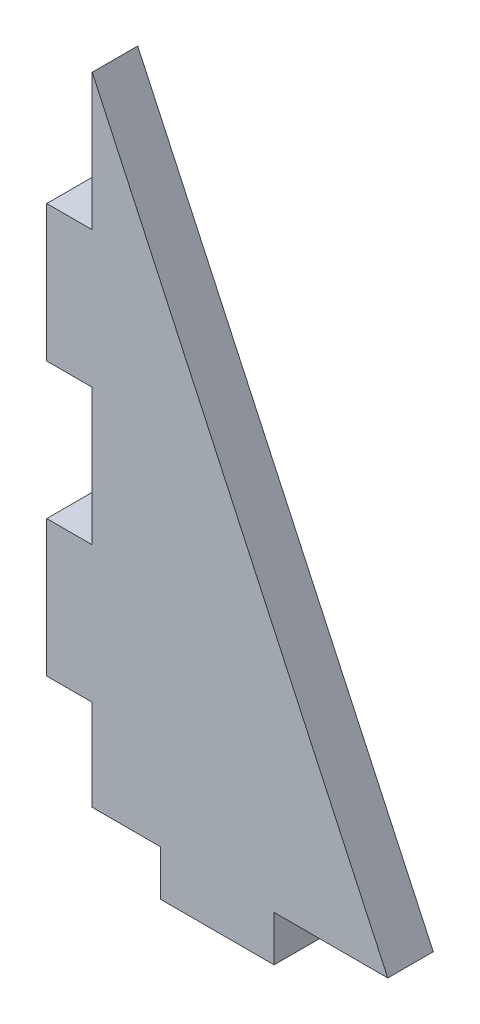
SolidWorks part; units mm, degrees
ref_plane "Front Plane" through (0, 0, 0) normal (0, 0, 1) x (1, 0, 0)
ref_plane "Top Plane" through (0, 0, 0) normal (0, 1, 0) x (1, 0, 0)
ref_plane "Right Plane" through (0, 0, 0) normal (1, 0, 0) x (0, 0, -1)
sketch "Sketch1" plane through (0, 0, 0) normal (0, 0, 1) x (1, 0, 0)
  line L12 (0, 0) -> (0, 76.2)
  line L16 (0, 76.2) -> (5.08, 76.2)
  line L18 (5.08, 76.2) -> (38.1, 5.08)
  line L19 (38.1, 5.08) -> (38.1, 0)
  line L20 (38.1, 0) -> (0, 0)
  dimension "D1" = 5.08
  dimension "D2" = 76.2
  dimension "D3" = 38.1
extrude "Boss-Extrude1" add sketch "Sketch1" along normal blind 5.08
sketch "Sketch2" plane through (0, 0, 5.08) normal (0, 0, 1) x (1, 0, 0)
  line L0 (5.08, 76.2) -> (5.08, 60.96)
  line L1 (5.08, 60.96) -> (5.08, 45.72) construction
  line L2 (5.08, 45.72) -> (5.08, 30.48)
  line L3 (5.08, 30.48) -> (5.08, 15.24) construction
  line L4 (5.08, 15.24) -> (5.08, 0)
  line L5 (0, 0) -> (38.1, 0) construction
  line L6 (5.08, 15.24) -> (0, 15.24)
  line L7 (0, 76.2) -> (0, 0) construction
  line L8 (5.08, 30.48) -> (0, 30.48)
  line L9 (5.08, 45.72) -> (0, 45.72)
  line L10 (5.08, 60.96) -> (0, 60.96)
  line L11 (5.08, 76.2) -> (0, 76.2)
  line L12 (0, 76.2) -> (0, 60.96)
  line L13 (0, 45.72) -> (0, 30.48)
  line L14 (0, 15.24) -> (0, 0)
  line L15 (0, 0) -> (5.08, 0)
  line L16 (38.1, 5.08) -> (25.4, 5.08)
  line L17 (25.4, 5.08) -> (12.7, 5.08) construction
  line L18 (12.7, 5.08) -> (0, 5.08)
  line L19 (12.7, 5.08) -> (12.7, 0)
  line L20 (25.4, 5.08) -> (25.4, 0)
  line L21 (12.7, 0) -> (0, 0)
  line L22 (25.4, 0) -> (38.1, 0)
  line L23 (38.1, 0) -> (38.1, 5.08)
  line M12 (0, 0) -> (38.1, 0)
  line M13 (38.1, 0) -> (38.1, 5.08)
  line M15 (5.08, 76.2) -> (0, 76.2)
  line M16 (0, 76.2) -> (0, 0)
extrude "Cut-Extrude1" cut sketch "Sketch2" against normal blind 5.08 contours L10 L0 M15 M16 | L2 L9 L8 M16 | L18 L4 L6 M16 | L4 L18 L14 M12 | L19 L18 L4 M12 | L16 L20 M12 M13
equation "\"TubeR\"= 0.8in"
equation "\"Foamcore\"= 0.2in"
equation "\"MDF\"= 0.2in"
equation "\"NutD\"= 0.2145in"
equation "\"NutH\"= 0.0915in"
equation "\"MountScrewL\"= 0.3in"
equation "\"MountScrewD\"= 3.6mm"
equation "\"D1@Sketch1\"=\"MDF\""
equation "\"D1@Boss-Extrude1\"=\"MDF\""
